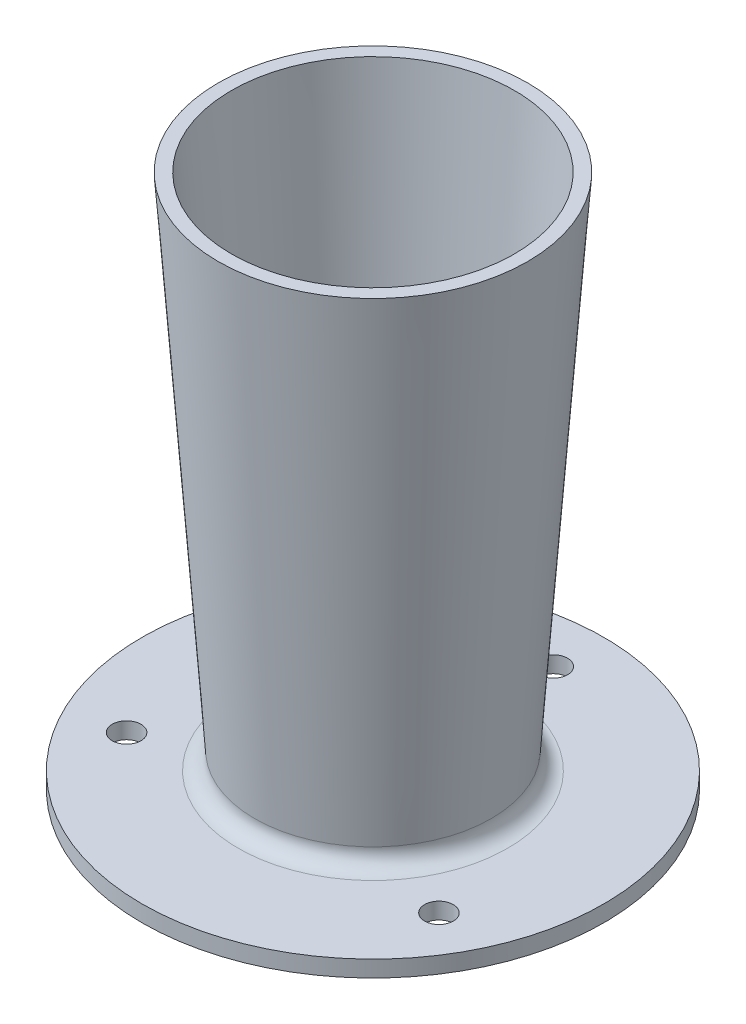
SolidWorks part; units mm, degrees
ref_plane "Front Plane" through (0, 0, 0) normal (0, 0, 1) x (1, 0, 0)
ref_plane "Top Plane" through (0, 0, 0) normal (0, 1, 0) x (1, 0, 0)
ref_plane "Right Plane" through (0, 0, 0) normal (1, 0, 0) x (0, 0, -1)
sketch "Sketch1" plane through (0, 0, 0) normal (0, 0, 1) x (1, 0, 0)
  line L0 (11.5, 0) -> (11.5, 20.2224)
  line L1 (55, 0) -> (-55, 0) construction
  line L2 (11.5, 20.2224) -> (14, 20.2224)
  line L3 (14, 20.2224) -> (17.273, 65.2224)
  line L4 (17.273, 65.2224) -> (18.8772, 65.2224)
  line L5 (18.8772, 65.2224) -> (14.2788, 2)
  line L8 (28.1712, 0) -> (11.5, 0)
  line L9 (0, -55) -> (0, 55) construction
  line L10 (0, 70.0735) -> (0, -30.6209) construction
  line L11 (28.1712, 0) -> (28.1712, 2)
  line L12 (28.1712, 2) -> (14.2788, 2)
  dimension "D1" = 11.5
  dimension "D2" = 2
  dimension "D4" = 1.6
  dimension "D5" = 94.16
  dimension "D6" = 14
  dimension "D7" = 45
revolve "Revolve1" add sketch "Sketch1" angle 360 about L10
fillet "Fillet1" radius 2 1 edges at (0, 2, 14.2788)
sketch "Sketch2" plane through (0, 2, 0) normal (0, 1, 0) x (1, 0, 0)
  line L0 (0, -30.9883) -> (0, 30.9883) construction
  circle A0 centre (0, 22) radius 1.75
  circle A1 centre (0, 0) radius 28.1712 construction
  circle A2 centre (19.0526, -11) radius 1.75
  circle A3 centre (-19.0526, -11) radius 1.75
  point P13 (0, 0)
  dimension "D1" = 3.5
  dimension "D2" = 22
  dimension "D3" = 3
extrude "Cut-Extrude1" cut sketch "Sketch2" against normal through all
